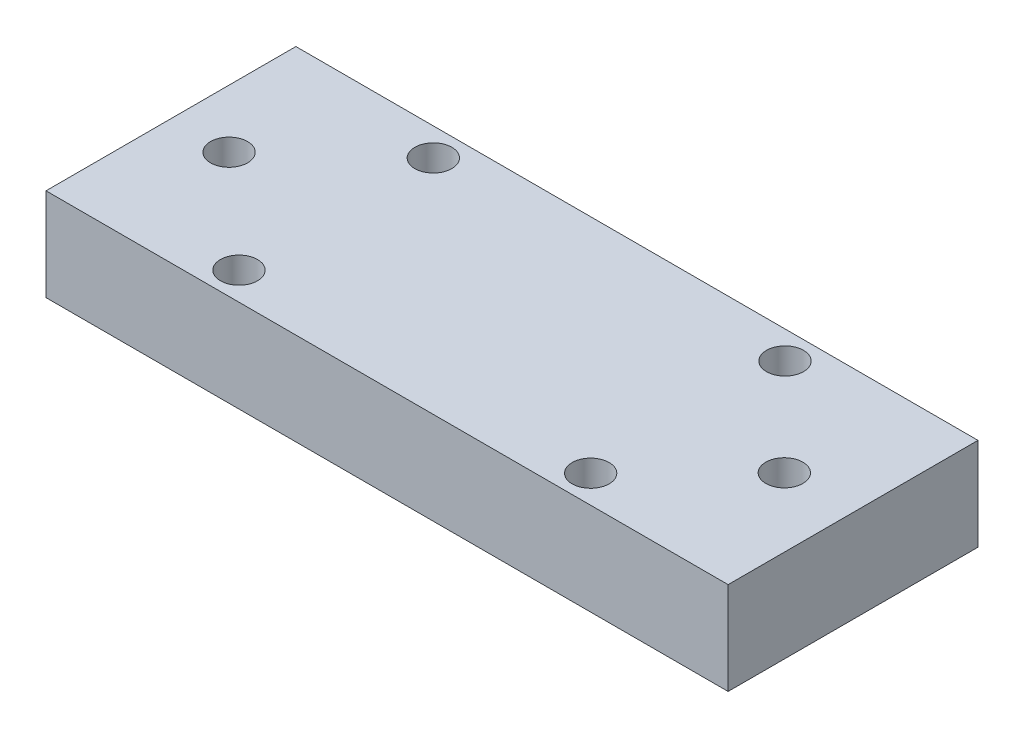
SolidWorks part; units mm, degrees
ref_plane "Front Plane" through (0, 0, 0) normal (0, 0, 1) x (1, 0, 0)
ref_plane "Top Plane" through (0, 0, 0) normal (0, 1, 0) x (1, 0, 0)
ref_plane "Right Plane" through (0, 0, 0) normal (1, 0, 0) x (0, 0, -1)
sketch "Sketch1" plane through (0, 0, 0) normal (0, 1, 0) x (1, 0, 0)
  line L1 (18.4264, -6.75) -> (-18.4264, -6.75)
  line L2 (18.4264, -6.75) -> (18.4264, 6.75)
  line L3 (18.4264, 6.75) -> (-18.4264, 6.75)
  line L4 (-18.4264, -6.75) -> (-18.4264, 6.75)
  line L5 (18.4264, -6.75) -> (-18.4264, 6.75) construction
  line L6 (18.4264, 6.75) -> (-18.4264, -6.75) construction
  line L7 (9.5, -5.25) -> (-9.5, -5.25) construction
  line L8 (9.5, -5.25) -> (9.5, 5.25) construction
  line L9 (9.5, 5.25) -> (-9.5, 5.25) construction
  line L10 (-9.5, -5.25) -> (-9.5, 5.25) construction
  line L11 (9.5, -5.25) -> (-9.5, 5.25) construction
  line L12 (9.5, 5.25) -> (-9.5, -5.25) construction
  circle A0 centre (-15.2865, 0) radius 1
  circle A1 centre (14.7135, 0) radius 1
  circle A2 centre (-9.5, 5.25) radius 1
  circle A3 centre (9.5, 5.25) radius 1
  circle A4 centre (9.5, -5.25) radius 1
  circle A5 centre (-9.5, -5.25) radius 1
  point P0 (0, 0)
  point P10 (0, 0)
  dimension "D2" = 2
  dimension "D3" = 2
  dimension "D7" = 2
  dimension "D1" = 30
  dimension "D4" = 19
  dimension "D5" = 10.5
  dimension "D6" = 13.5
extrude "Boss-Extrude1" add sketch "Sketch1" along normal blind 5 contours L2 L1 L4 L3 | A0 | A5 | A2 | A1 | A4 | A3
